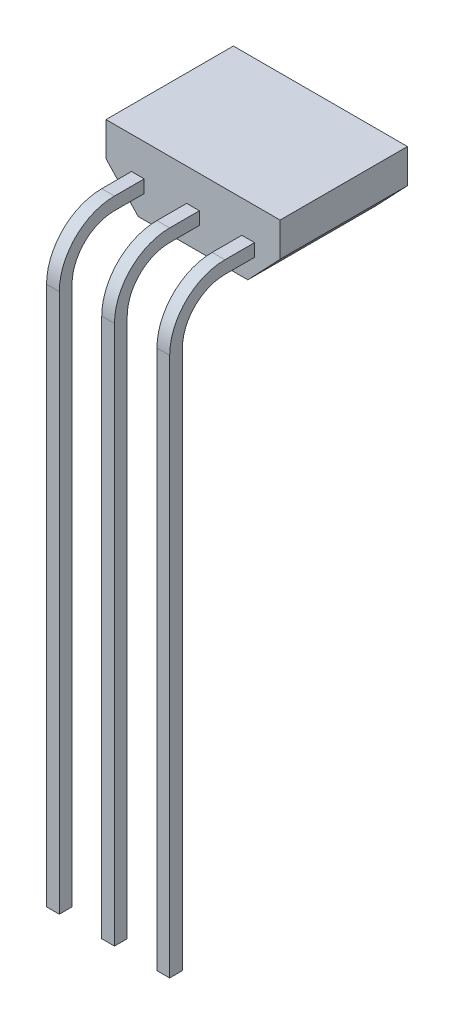
SolidWorks part; units mm, degrees
ref_plane "Спереди" through (0, 0, 0) normal (0, 0, 1) x (1, 0, 0)
ref_plane "Сверху" through (0, 0, 0) normal (0, 1, 0) x (1, 0, 0)
ref_plane "Справа" through (0, 0, 0) normal (1, 0, 0) x (0, 0, -1)
sketch "Эскиз1" plane through (0, 0, 0) normal (0, 1, 0) x (1, 0, 0)
  line L1 (2.05, -1.5) -> (-2.05, -1.5)
  line L2 (2.05, -1.5) -> (2.05, 1.5)
  line L3 (2.05, 1.5) -> (-2.05, 1.5)
  line L4 (-2.05, -1.5) -> (-2.05, 1.5)
  line L5 (2.05, -1.5) -> (-2.05, 1.5) construction
  line L6 (2.05, 1.5) -> (-2.05, -1.5) construction
  point P0 (0, 0)
  dimension "D1" = 3
  dimension "D2" = 4.1
extrude "Бобышка-Вытянуть1" add sketch "Эскиз1" along normal blind 1.6
chamfer "Фаска1" distance 0.76 distance2 0.8 2 edges at (-2.05, 0, 0) (2.05, 0, 0)
sketch "Эскиз2" plane through (0, 0, 0) normal (1, 0, 0) x (0, 0, -1)
  line L0 (-2.2, 0.84) -> (-1.5, 0.84)
  line L2 (-1.5, 0.84) -> (-1.5, 0.54)
  line L3 (-1.5, 0.54) -> (-2.2, 0.54)
  line L6 (-3.5, -0.46) -> (-3.5, -13.16)
  line L7 (-3.5, -13.16) -> (-3.2, -13.16)
  line L8 (-3.2, -0.46) -> (-3.2, -13.16)
  line L9 (-1.5, 1.6) -> (-1.5, 0.8) construction
  line L11 (-1.5, 1.6) -> (1.5, 1.6) construction
  arc A0 (-3.2, -0.46) -> (-2.2, 0.54) centre (-2.2, -0.46) cw
  arc A1 (-2.2, 0.84) -> (-3.5, -0.46) centre (-2.2, -0.46) ccw
  point P12 (0, 0)
  point P13 (-3.5, 0.84)
  point P14 (0, 0)
  point P15 (0, 0)
  point P19 (0, 0)
  point P20 (0, 0)
  dimension "D4" = 0.3
  dimension "D5" = 1.3
  dimension "D6" = 1
  dimension "D1" = 0.3
  dimension "D2" = 2
  dimension "D3" = 14
  dimension "D7" = 0.76
extrude "Бобышка-Вытянуть2" add sketch "Эскиз2" along normal mid plane 0.3
pattern_linear "Линейный массив1" count 2 spacing 1.3 along (-1, 0, 0) of "Бобышка-Вытянуть2"
mirror "Зеркальное отражение1" about plane through (0, 0, 0) normal (1, 0, 0) of "Линейный массив1"
